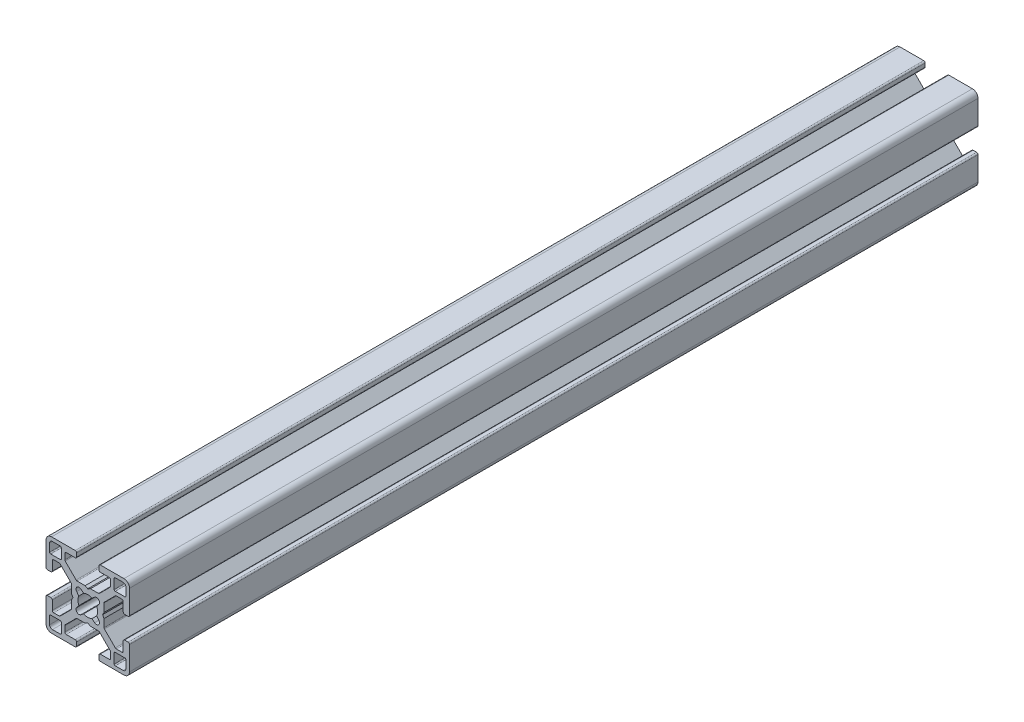
SolidWorks part; units mm, degrees
material "6105-T5 Aluminum"
ref_plane "Front Plane" through (0, 0, 0) normal (0, 0, 1) x (1, 0, 0)
ref_plane "Top Plane" through (0, 0, 0) normal (0, 1, 0) x (1, 0, 0)
ref_plane "Right Plane" through (0, 0, 0) normal (1, 0, 0) x (0, 0, -1)
sketch "Sketch1" plane through (0, 0, 0) normal (0, 0, 1) x (1, 0, 0)
  line L0 (9.5, -13.3189) -> (9.5, -9.88)
  line L1 (9.88, -9.5) -> (13.3189, -9.5)
  line L2 (13.6999, -9.881) -> (13.6999, -12.6999)
  line L3 (12.6999, -13.6999) -> (9.881, -13.6999)
  line L4 (-13.3189, -9.5) -> (-9.88, -9.5)
  line L5 (-9.5, -9.88) -> (-9.5, -13.3189)
  line L6 (-9.881, -13.6999) -> (-12.6999, -13.6999)
  line L7 (-13.6999, -12.6999) -> (-13.6999, -9.881)
  line L8 (-1.4942, -3.1981) -> (-2.4733, -3.9799)
  line L9 (-3.9799, -2.4733) -> (-3.1981, -1.4942)
  line L10 (-3.1981, 1.4942) -> (-3.9799, 2.4733)
  line L11 (-2.4733, 3.9799) -> (-1.4942, 3.1981)
  line L12 (1.4942, 3.1981) -> (2.4733, 3.9799)
  line L13 (3.9799, 2.4733) -> (3.1981, 1.4942)
  line L14 (3.1981, -1.4942) -> (3.9799, -2.4733)
  line L15 (2.4733, -3.9799) -> (1.4942, -3.1981)
  line L16 (-9.5, 13.3189) -> (-9.5, 9.88)
  line L17 (-9.88, 9.5) -> (-13.3189, 9.5)
  line L18 (-13.6999, 9.881) -> (-13.6999, 12.6999)
  line L19 (-12.6999, 13.6999) -> (-9.881, 13.6999)
  line L20 (9.881, 13.6999) -> (12.6999, 13.6999)
  line L21 (13.6999, 12.6999) -> (13.6999, 9.881)
  line L22 (13.3189, 9.5) -> (9.88, 9.5)
  line L23 (9.5, 9.88) -> (9.5, 13.3189)
  line L24 (12.7425, -4.5) -> (12.7425, -7.7325)
  line L25 (12.2428, -8.25) -> (10.2602, -8.25)
  line L26 (9.9066, -8.1035) -> (5.9811, -4.178)
  line L27 (5.8347, -3.8245) -> (5.8347, -1.0125)
  line L28 (5.8347, -1.0125) -> (5.3247, -0.0625)
  line L29 (5.3247, -0.0625) -> (5.8347, 0.8875)
  line L30 (5.8347, 0.8875) -> (5.8347, 3.8245)
  line L31 (5.9811, 4.178) -> (9.9066, 8.1035)
  line L32 (10.2602, 8.25) -> (12.2428, 8.25)
  line L33 (12.7425, 7.7325) -> (12.7425, 4.5)
  line L34 (13.2425, 4) -> (14.4999, 4)
  line L35 (14.9999, 4.5) -> (14.9999, 12.9999)
  line L36 (12.9999, 14.9999) -> (4.5, 14.9999)
  line L37 (4, 14.4999) -> (4, 13.2425)
  line L38 (4.5, 12.7425) -> (7.7325, 12.7425)
  line L39 (8.25, 12.2428) -> (8.25, 10.2602)
  line L40 (8.1035, 9.9066) -> (4.178, 5.9811)
  line L41 (3.8245, 5.8347) -> (0.95, 5.8347)
  line L42 (0.95, 5.8347) -> (0, 5.3247)
  line L43 (0, 5.3247) -> (-0.95, 5.8347)
  line L44 (-0.95, 5.8347) -> (-3.8245, 5.8347)
  line L45 (-4.178, 5.9811) -> (-8.1035, 9.9066)
  line L46 (-8.25, 10.2602) -> (-8.25, 12.2428)
  line L47 (-7.7325, 12.7425) -> (-4.5, 12.7425)
  line L48 (-4, 13.2425) -> (-4, 14.4999)
  line L49 (-4.5, 14.9999) -> (-12.9999, 14.9999)
  line L50 (-14.9999, 12.9999) -> (-14.9999, 4.5)
  line L51 (-14.4999, 4) -> (-13.2425, 4)
  line L52 (-12.7425, 4.5) -> (-12.7425, 7.7325)
  line L53 (-12.2428, 8.25) -> (-10.2602, 8.25)
  line L54 (-9.9066, 8.1035) -> (-5.9811, 4.178)
  line L55 (-5.8347, 3.8245) -> (-5.8347, 0.8875)
  line L56 (-5.8347, 0.8875) -> (-5.3247, -0.0625)
  line L57 (-5.3247, -0.0625) -> (-5.8347, -1.0125)
  line L58 (-5.8347, -1.0125) -> (-5.8347, -3.8245)
  line L59 (-5.9811, -4.178) -> (-9.9066, -8.1035)
  line L60 (-10.2602, -8.25) -> (-12.2428, -8.25)
  line L61 (-12.7425, -7.7325) -> (-12.7425, -4.5)
  line L62 (-13.2425, -4) -> (-14.4999, -4)
  line L63 (-14.9999, -4.5) -> (-14.9999, -12.9999)
  line L64 (-12.9999, -14.9999) -> (-4.5, -14.9999)
  line L65 (-4, -14.4999) -> (-4, -13.2425)
  line L66 (-4.5, -12.7425) -> (-7.7325, -12.7425)
  line L67 (-8.25, -12.2428) -> (-8.25, -10.2602)
  line L68 (-8.1035, -9.9066) -> (-4.178, -5.9811)
  line L69 (-3.8245, -5.8347) -> (-0.95, -5.8347)
  line L70 (-0.95, -5.8347) -> (0, -5.3247)
  line L71 (0, -5.3247) -> (0.95, -5.8347)
  line L72 (0.95, -5.8347) -> (3.8245, -5.8347)
  line L73 (4.178, -5.9811) -> (8.1035, -9.9066)
  line L74 (8.25, -10.2602) -> (8.25, -12.2428)
  line L75 (7.7325, -12.7425) -> (4.5, -12.7425)
  line L76 (4, -13.2425) -> (4, -14.4999)
  line L77 (4.5, -14.9999) -> (12.9999, -14.9999)
  line L78 (14.9999, -12.9999) -> (14.9999, -4.5)
  line L79 (14.4999, -4) -> (13.2425, -4)
  arc A0 (9.5, -13.3189) -> (9.881, -13.6999) centre (9.881, -13.3189) ccw
  arc A1 (9.88, -9.5) -> (9.5, -9.88) centre (9.88, -9.88) ccw
  arc A2 (13.6999, -9.881) -> (13.3189, -9.5) centre (13.3189, -9.881) ccw
  arc A3 (12.6999, -13.6999) -> (13.6999, -12.6999) centre (12.6999, -12.6999) ccw
  arc A4 (-13.3189, -9.5) -> (-13.6999, -9.881) centre (-13.3189, -9.881) ccw
  arc A5 (-9.5, -9.88) -> (-9.88, -9.5) centre (-9.88, -9.88) ccw
  arc A6 (-9.881, -13.6999) -> (-9.5, -13.3189) centre (-9.881, -13.3189) ccw
  arc A7 (-13.6999, -12.6999) -> (-12.6999, -13.6999) centre (-12.6999, -12.6999) ccw
  arc A8 (-1.4942, -3.1981) -> (1.4942, -3.1981) centre (0, 0) ccw
  arc A9 (-3.9799, -2.4733) -> (-2.4733, -3.9799) centre (-3.1422, -3.1422) ccw
  arc A10 (-3.1981, 1.4942) -> (-3.1981, -1.4942) centre (0, 0) ccw
  arc A11 (-2.4733, 3.9799) -> (-3.9799, 2.4733) centre (-3.1422, 3.1422) ccw
  arc A12 (1.4942, 3.1981) -> (-1.4942, 3.1981) centre (0, 0) ccw
  arc A13 (3.9799, 2.4733) -> (2.4733, 3.9799) centre (3.1422, 3.1422) ccw
  arc A14 (3.1981, -1.4942) -> (3.1981, 1.4942) centre (0, 0) ccw
  arc A15 (2.4733, -3.9799) -> (3.9799, -2.4733) centre (3.1422, -3.1422) ccw
  arc A16 (-9.5, 13.3189) -> (-9.881, 13.6999) centre (-9.881, 13.3189) ccw
  arc A17 (-9.88, 9.5) -> (-9.5, 9.88) centre (-9.88, 9.88) ccw
  arc A18 (-13.6999, 9.881) -> (-13.3189, 9.5) centre (-13.3189, 9.881) ccw
  arc A19 (-12.6999, 13.6999) -> (-13.6999, 12.6999) centre (-12.6999, 12.6999) ccw
  arc A20 (9.881, 13.6999) -> (9.5, 13.3189) centre (9.881, 13.3189) ccw
  arc A21 (13.6999, 12.6999) -> (12.6999, 13.6999) centre (12.6999, 12.6999) ccw
  arc A22 (13.3189, 9.5) -> (13.6999, 9.881) centre (13.3189, 9.881) ccw
  arc A23 (9.5, 9.88) -> (9.88, 9.5) centre (9.88, 9.88) ccw
  arc A24 (13.2425, -4) -> (12.7425, -4.5) centre (13.2425, -4.5) ccw
  arc A25 (12.2428, -8.25) -> (12.7425, -7.7325) centre (12.2428, -7.75) ccw
  arc A26 (9.9066, -8.1035) -> (10.2602, -8.25) centre (10.2602, -7.75) ccw
  arc A27 (5.8347, -3.8245) -> (5.9811, -4.178) centre (6.3347, -3.8245) ccw
  arc A28 (5.9811, 4.178) -> (5.8347, 3.8245) centre (6.3347, 3.8245) ccw
  arc A29 (10.2602, 8.25) -> (9.9066, 8.1035) centre (10.2602, 7.75) ccw
  arc A30 (12.7425, 7.7325) -> (12.2428, 8.25) centre (12.2428, 7.75) ccw
  arc A31 (12.7425, 4.5) -> (13.2425, 4) centre (13.2425, 4.5) ccw
  arc A32 (14.4999, 4) -> (14.9999, 4.5) centre (14.4999, 4.5) ccw
  arc A33 (14.9999, 12.9999) -> (12.9999, 14.9999) centre (12.9999, 12.9999) ccw
  arc A34 (4.5, 14.9999) -> (4, 14.4999) centre (4.5, 14.4999) ccw
  arc A35 (4, 13.2425) -> (4.5, 12.7425) centre (4.5, 13.2425) ccw
  arc A36 (8.25, 12.2428) -> (7.7325, 12.7425) centre (7.75, 12.2428) ccw
  arc A37 (8.1035, 9.9066) -> (8.25, 10.2602) centre (7.75, 10.2602) ccw
  arc A38 (3.8245, 5.8347) -> (4.178, 5.9811) centre (3.8245, 6.3347) ccw
  arc A39 (-4.178, 5.9811) -> (-3.8245, 5.8347) centre (-3.8245, 6.3347) ccw
  arc A40 (-8.25, 10.2602) -> (-8.1035, 9.9066) centre (-7.75, 10.2602) ccw
  arc A41 (-7.7325, 12.7425) -> (-8.25, 12.2428) centre (-7.75, 12.2428) ccw
  arc A42 (-4.5, 12.7425) -> (-4, 13.2425) centre (-4.5, 13.2425) ccw
  arc A43 (-4, 14.4999) -> (-4.5, 14.9999) centre (-4.5, 14.4999) ccw
  arc A44 (-12.9999, 14.9999) -> (-14.9999, 12.9999) centre (-12.9999, 12.9999) ccw
  arc A45 (-14.9999, 4.5) -> (-14.4999, 4) centre (-14.4999, 4.5) ccw
  arc A46 (-13.2425, 4) -> (-12.7425, 4.5) centre (-13.2425, 4.5) ccw
  arc A47 (-12.2428, 8.25) -> (-12.7425, 7.7325) centre (-12.2428, 7.75) ccw
  arc A48 (-9.9066, 8.1035) -> (-10.2602, 8.25) centre (-10.2602, 7.75) ccw
  arc A49 (-5.8347, 3.8245) -> (-5.9811, 4.178) centre (-6.3347, 3.8245) ccw
  arc A50 (-5.9811, -4.178) -> (-5.8347, -3.8245) centre (-6.3347, -3.8245) ccw
  arc A51 (-10.2602, -8.25) -> (-9.9066, -8.1035) centre (-10.2602, -7.75) ccw
  arc A52 (-12.7425, -7.7325) -> (-12.2428, -8.25) centre (-12.2428, -7.75) ccw
  arc A53 (-12.7425, -4.5) -> (-13.2425, -4) centre (-13.2425, -4.5) ccw
  arc A54 (-14.4999, -4) -> (-14.9999, -4.5) centre (-14.4999, -4.5) ccw
  arc A55 (-14.9999, -12.9999) -> (-12.9999, -14.9999) centre (-12.9999, -12.9999) ccw
  arc A56 (-4.5, -14.9999) -> (-4, -14.4999) centre (-4.5, -14.4999) ccw
  arc A57 (-4, -13.2425) -> (-4.5, -12.7425) centre (-4.5, -13.2425) ccw
  arc A58 (-8.25, -12.2428) -> (-7.7325, -12.7425) centre (-7.75, -12.2428) ccw
  arc A59 (-8.1035, -9.9066) -> (-8.25, -10.2602) centre (-7.75, -10.2602) ccw
  arc A60 (-3.8245, -5.8347) -> (-4.178, -5.9811) centre (-3.8245, -6.3347) ccw
  arc A61 (4.178, -5.9811) -> (3.8245, -5.8347) centre (3.8245, -6.3347) ccw
  arc A62 (8.25, -10.2602) -> (8.1035, -9.9066) centre (7.75, -10.2602) ccw
  arc A63 (7.7325, -12.7425) -> (8.25, -12.2428) centre (7.75, -12.2428) ccw
  arc A64 (4.5, -12.7425) -> (4, -13.2425) centre (4.5, -13.2425) ccw
  arc A65 (4, -14.4999) -> (4.5, -14.9999) centre (4.5, -14.4999) ccw
  arc A66 (12.9999, -14.9999) -> (14.9999, -12.9999) centre (12.9999, -12.9999) ccw
  arc A67 (14.9999, -4.5) -> (14.4999, -4) centre (14.4999, -4.5) ccw
extrude "Extrude1" add sketch "Sketch1" against normal blind 304.8
